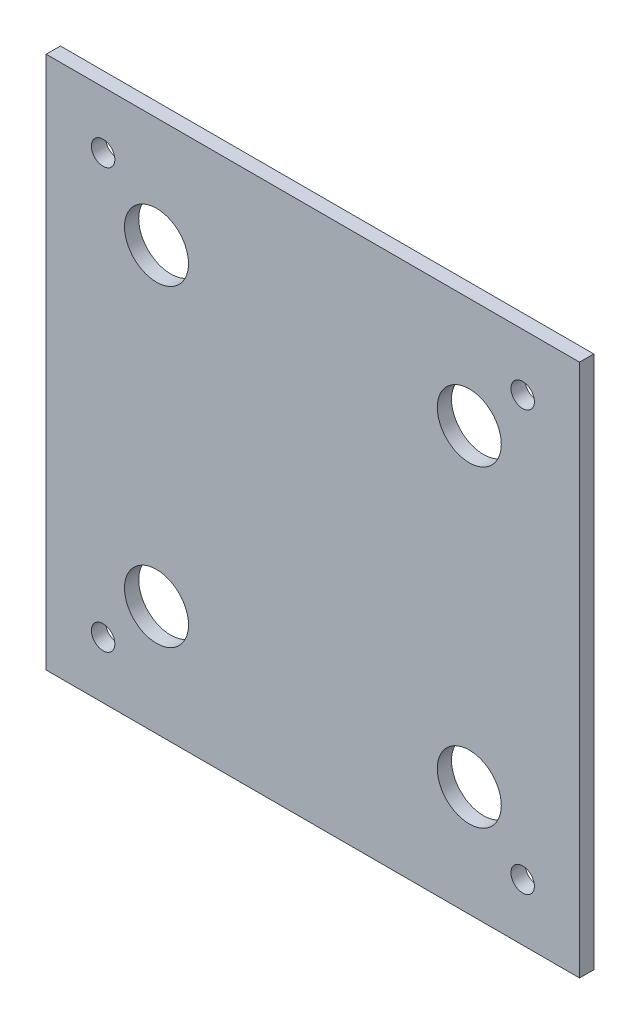
SolidWorks part; units mm, degrees
ref_plane "正面" through (0, 0, 0) normal (0, 0, 1) x (1, 0, 0)
ref_plane "平面" through (0, 0, 0) normal (0, 1, 0) x (1, 0, 0)
ref_plane "右側面" through (0, 0, 0) normal (1, 0, 0) x (0, 0, -1)
sketch "ｽｹｯﾁ1" plane through (0, 0, 0) normal (0, 0, 1) x (1, 0, 0)
  line L1 (-37.5, 37.5) -> (37.5, 37.5)
  line L2 (-37.5, 37.5) -> (-37.5, -37.5)
  line L3 (-37.5, -37.5) -> (37.5, -37.5)
  line L4 (37.5, 37.5) -> (37.5, -37.5)
  line L5 (-37.5, 37.5) -> (37.5, -37.5) construction
  line L6 (-37.5, -37.5) -> (37.5, 37.5) construction
  point P0 (0, 0)
  dimension "D1" = 75
  dimension "D2" = 75
extrude "ﾎﾞｽ - 押し出し1" add sketch "ｽｹｯﾁ1" along normal blind 2
sketch "ｽｹｯﾁ2" plane through (0, 0, 0) normal (0, 0, -1) x (-1, 0, 0)
  line L0 (-37.5, -37.5) -> (-37.5, 37.5) construction
  line L1 (37.5, -37.5) -> (29.5, -37.5)
  line L2 (37.5, -37.5) -> (37.5, -29.5)
  line L3 (37.5, -29.5) -> (29.5, -29.5)
  line L4 (29.5, -37.5) -> (29.5, -29.5)
  line L5 (37.5, 37.5) -> (29.5, 37.5)
  line L6 (37.5, 37.5) -> (37.5, 29.5)
  line L7 (37.5, 29.5) -> (29.5, 29.5)
  line L8 (29.5, 37.5) -> (29.5, 29.5)
  line L9 (-37.5, 37.5) -> (-29.5, 37.5)
  line L10 (-37.5, 37.5) -> (-37.5, 29.5)
  line L11 (-37.5, 29.5) -> (-29.5, 29.5)
  line L12 (-29.5, 37.5) -> (-29.5, 29.5)
  line L13 (-37.5, -37.5) -> (-29.5, -37.5)
  line L14 (-37.5, -37.5) -> (-37.5, -29.5)
  line L15 (-37.5, -29.5) -> (-29.5, -29.5)
  line L16 (-29.5, -37.5) -> (-29.5, -29.5)
  line L17 (37.5, -37.5) -> (-37.5, -37.5) construction
  circle A0 centre (29.5, -29.5) radius 4.0722
  circle A1 centre (29.5, 29.5) radius 5.8197
  circle A2 centre (-29.5, 29.5) radius 4.0406
  circle A3 centre (-29.5, -29.5) radius 4.8058
  dimension "D1" = 8
  dimension "D2" = 8
  dimension "D3" = 8
  dimension "D4" = 8
  dimension "D5" = 8
  dimension "D6" = 8
  dimension "D7" = 8
  dimension "D8" = 8
hole_wizard "M4x0.7 ねじ穴1" positions "3Dｽｹｯﾁ2" profile "ｽｹｯﾁ4" tap size "M4x0.7" standard "JIS"
sketch3d "3Dｽｹｯﾁ2"
  point P0 (-29.5, -29.5, 0)
  point P3 (-29.5, 29.5, 0)
  point P6 (29.5, 29.5, 0)
  point P9 (29.5, -29.5, 0)
sketch "ｽｹｯﾁ4" plane through (-29.5, -29.5, 0) normal (1, 0, 0) x (0, 1, 0)
  line L0 (0, 0) -> (0, 12.4914)
  line L1 (0, 12.4914) -> (1.65, 11.5)
  line L2 (1.65, 11.5) -> (1.65, 0)
  line L5 (1.65, 0) -> (0, 0)
  line L10 (0, 12.4914) -> (-1.65, 11.5) construction
  line L11 (0, -6.35) -> (0, 107.95) construction
  dimension "ねじ下穴ﾄﾞﾘﾙ直径" = 3.3
  dimension "ねじ下穴ﾄﾞﾘﾙの深さ" = 11.5
  dimension "ﾄﾞﾘﾙ角度" = 118
cosmetic thread "穴のねじ山1" parameters "D1"=2, "D2"=4
cosmetic thread "穴のねじ山2" parameters "D1"=2, "D2"=4
cosmetic thread "穴のねじ山3" parameters "D1"=2, "D2"=4
cosmetic thread "穴のねじ山4" parameters "D1"=2, "D2"=4
sketch "ｽｹｯﾁ5" plane through (0, 0, 0) normal (0, 0, -1) x (-1, 0, 0)
  line L0 (0, 0) -> (-21.991, -21.991)
  line L2 (21.991, 21.991) -> (-21.991, 21.991)
  line L3 (21.991, 21.991) -> (21.991, -21.991)
  line L4 (21.991, -21.991) -> (-21.991, -21.991)
  line L5 (-21.991, 21.991) -> (-21.991, -21.991)
  line L6 (21.991, 21.991) -> (-21.991, -21.991) construction
  line L7 (21.991, -21.991) -> (-21.991, 21.991) construction
  circle A0 centre (21.991, -21.991) radius 4.5
  circle A1 centre (21.991, 21.991) radius 4.5
  circle A2 centre (-21.991, -21.991) radius 4.5
  circle A3 centre (-21.991, 21.991) radius 4.5
  dimension "D2" = 9
  dimension "D3" = 9
  dimension "D4" = 9
  dimension "D5" = 9
  dimension "D1" = 31.1
extrude "ｶｯﾄ - 押し出し1" cut sketch "ｽｹｯﾁ5" against normal blind 80 contours L4 A0 L3 | L3 A0 L4 | L3 A1 L2 | L2 A1 L3 | L2 A3 L5 | L5 A3 L2 | L5 A2 L4 | L0 A2 L5 | L4 A2 L0
sketch "ｽｹｯﾁ6" plane through (0, 0, 0) normal (0, 0, -1) x (-1, 0, 0)
  line L1 (21.991, -21.991) -> (-21.991, -21.991)
  line L2 (21.991, -21.991) -> (21.991, 21.991)
  line L3 (21.991, 21.991) -> (-21.991, 21.991)
  line L4 (-21.991, -21.991) -> (-21.991, 21.991)
  line L5 (21.991, -21.991) -> (-21.991, 21.991) construction
  line L6 (21.991, 21.991) -> (-21.991, -21.991) construction
  line L7 (29.5, -29.5) -> (-29.5, -29.5)
  line L8 (29.5, -29.5) -> (29.5, 29.5)
  line L9 (29.5, 29.5) -> (-29.5, 29.5)
  line L10 (-29.5, -29.5) -> (-29.5, 29.5)
  line L11 (29.5, -29.5) -> (-29.5, 29.5) construction
  line L12 (29.5, 29.5) -> (-29.5, -29.5) construction
  circle A0 centre (29.5, -29.5) radius 4
  circle A1 centre (21.991, -21.991) radius 4
  circle A2 centre (21.991, 21.991) radius 4
  circle A3 centre (29.5, 29.5) radius 4
  circle A4 centre (-21.991, -21.991) radius 8.3706
  circle A5 centre (-29.5, -29.5) radius 4
  circle A6 centre (-21.991, 21.991) radius 6.7493
  circle A7 centre (-29.5, 29.5) radius 6.899
  point P0 (0, 0)
  point P7 (0, 0)
  dimension "D3" = 8
  dimension "D4" = 8
  dimension "D5" = 8
  dimension "D6" = 8
  dimension "D7" = 8
  dimension "D8" = 16.7412
  dimension "D1" = 59
  dimension "D2" = 43.982
